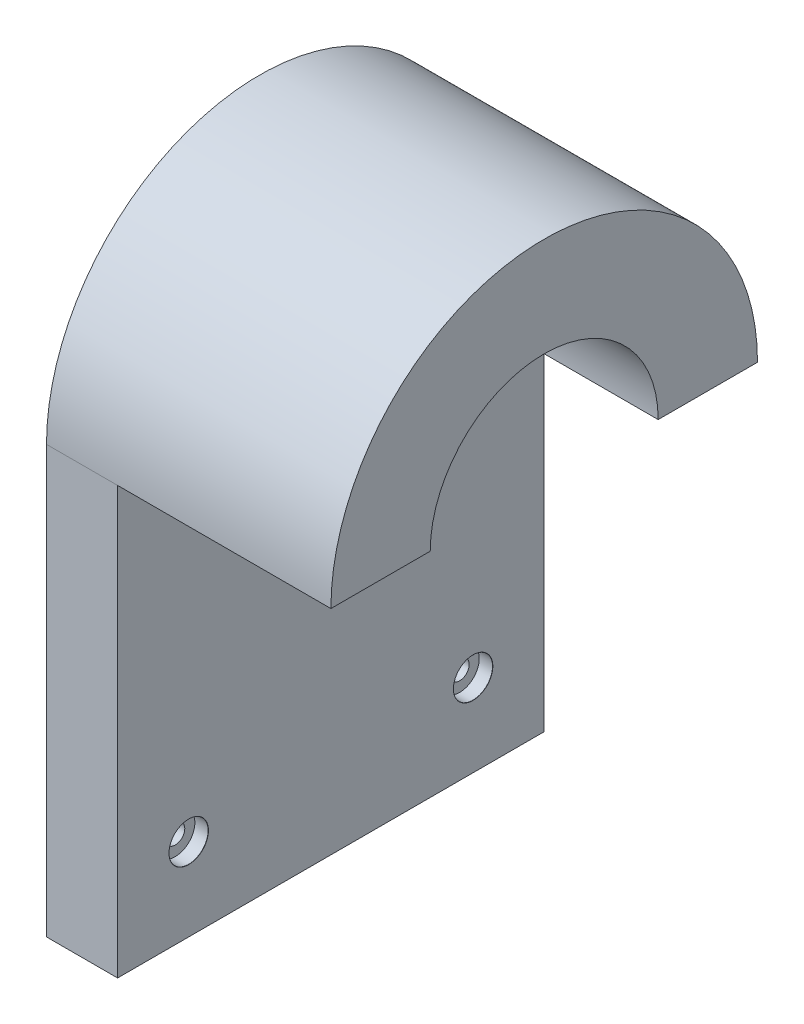
SolidWorks part; units mm, degrees
ref_plane "Front Plane" through (0, 0, 0) normal (0, 0, 1) x (1, 0, 0)
ref_plane "Top Plane" through (0, 0, 0) normal (0, 1, 0) x (1, 0, 0)
ref_plane "Right Plane" through (0, 0, 0) normal (1, 0, 0) x (0, 0, -1)
sketch "Sketch1" plane through (0, 0, 0) normal (1, 0, 0) x (0, 0, -1)
  line L0 (-38.1, 0) -> (-38.1, -76.2)
  line L1 (-38.1, -76.2) -> (38.1, -76.2)
  line L2 (38.1, -76.2) -> (38.1, 0)
  circle A0 centre (0, 0) radius 38.1
  dimension "D1" = 76.2
extrude "Boss-Extrude3" add sketch "Sketch1" along normal blind 12.7 contours A0 L0 L1 L2
sketch "Sketch5" plane through (12.7, 0, 0) normal (1, 0, 0) x (0, 0, -1)
  line L0 (-38.1, 0) -> (38.1, 0)
  circle A0 centre (0, 0) radius 38.1
  circle A1 centre (0, 0) radius 20.3584
  arc M2 (38.1, 0) -> (-38.1, 0) centre (0, 0) ccw
extrude "Boss-Extrude4" add sketch "Sketch5" along normal blind 38.1 contours A1 L0 M2
sketch "Sketch6" plane through (12.7, 0, 0) normal (1, 0, 0) x (0, 0, -1)
  line L0 (-38.1, -61.4783) -> (38.1, -61.4783)
  line L1 (-38.1, 0) -> (-38.1, -76.2) construction
  line L2 (38.1, -76.2) -> (38.1, 0) construction
  line L3 (-25.4, -61.4783) -> (-25.4, -76.2)
  line L4 (-38.1, -76.2) -> (38.1, -76.2) construction
  line L5 (25.4, -61.4783) -> (25.4, -76.2)
  dimension "D1" = 12.7
  dimension "D2" = 12.7
hole_wizard "CBORE for M3 Pan Head Machine Screw1" positions "Sketch7" profile "Sketch8" counterbore size "M3" standard "ANSI Metric" end condition through all
sketch "Sketch7" plane through (12.7, 0, 0) normal (1, 0, 0) x (0, 0, -1)
  point P0 (0, 0)
  point P3 (-25.4, -61.4783)
  point P6 (25.4, -61.4783)
sketch "Sketch8" plane through (12.7, 0, 0) normal (0, 1, 0) x (0, 0, -1)
  line L0 (0, 0) -> (0, 12.7)
  line L1 (0, 12.7) -> (1.7, 12.7)
  line L3 (1.7, 12.7) -> (1.7, 2.4)
  line L4 (3.5, 2.4) -> (1.7, 2.4)
  line L5 (3.5, 2.4) -> (3.5, 0.025)
  line L6 (3.5, 0.025) -> (3.525, 0)
  line L7 (3.525, 0) -> (0, 0)
  line L8 (-3.5, 0.025) -> (-3.525, 0) construction
  line L11 (0, -6.35) -> (0, 107.95) construction
  dimension "Thru Hole Dia." = 3.4
  dimension "Thru Hole Depth" = 12.7
  dimension "C'Bore Dia." = 7
  dimension "C'Bore Depth" = 2.4
  dimension "Near C'Sink Dia." = 7.05
  dimension "Near C'Sink Angle" = 90
